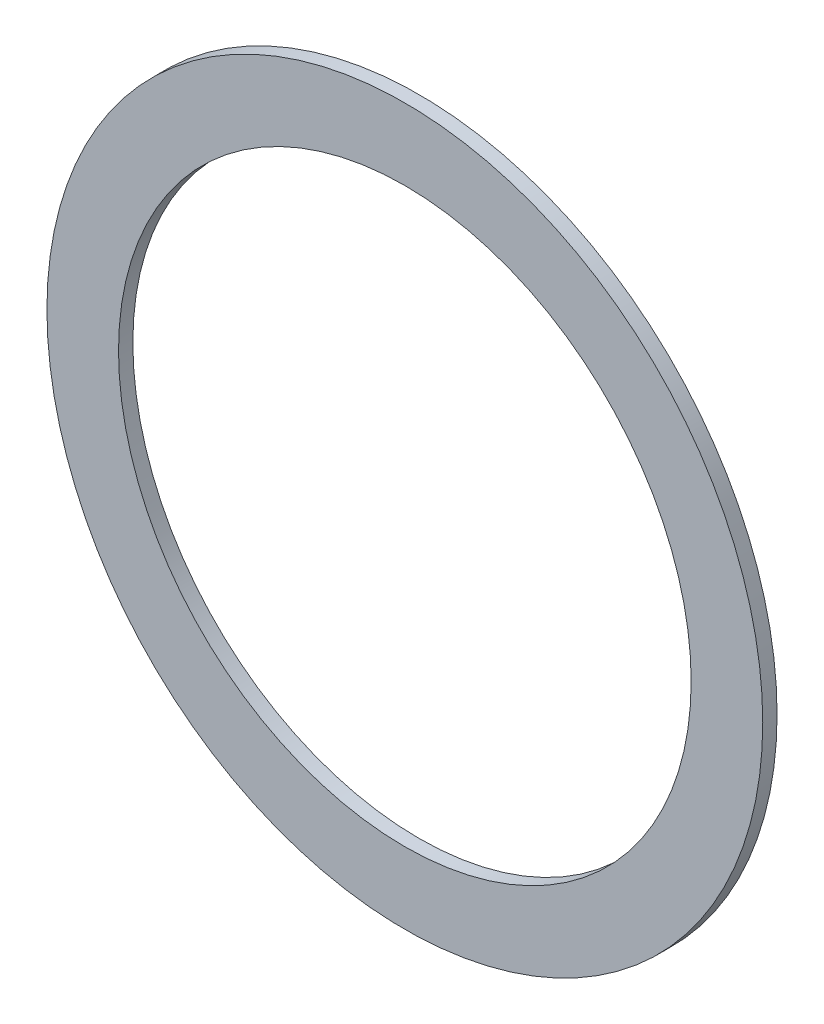
SolidWorks part; units mm, degrees
ref_plane "Plane1" through (0, 0, 0) normal (0, 0, 1) x (1, 0, 0)
ref_plane "Plane2" through (0, 0, 0) normal (0, 1, 0) x (1, 0, 0)
ref_plane "Plane3" through (0, 0, 0) normal (1, 0, 0) x (0, 0, -1)
sketch "Sketch1" plane through (0, 0, 0) normal (0, 0, 1) x (1, 0, 0)
  circle A0 centre (0, 0) radius 25
  circle A1 centre (0, 0) radius 20
  dimension "Indv. dia." = 40
  dimension "Udv. dia." = 50
extrude "Base-Extrude" add sketch "Sketch1" along normal blind 1
